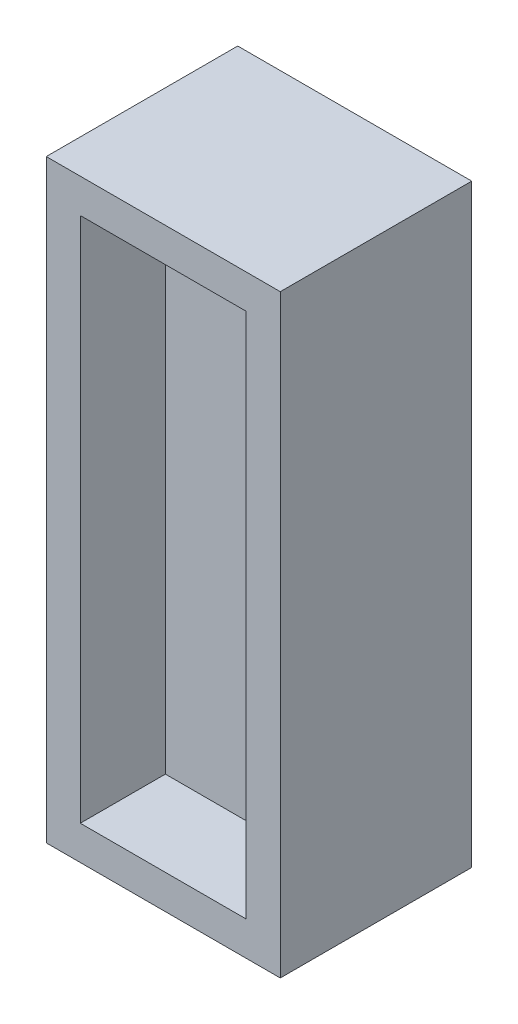
SolidWorks part; units mm, degrees
ref_plane "Front" through (0, 0, 0) normal (0, 0, 1) x (1, 0, 0)
ref_plane "Top" through (0, 0, 0) normal (0, 1, 0) x (1, 0, 0)
ref_plane "Right" through (0, 0, 0) normal (1, 0, 0) x (0, 0, -1)
sketch "Sketch1" plane through (0, 0, 0) normal (0, 0, 1) x (1, 0, 0)
  line L1 (27.5, -69.85) -> (-27.5, -69.85)
  line L2 (27.5, -69.85) -> (27.5, 69.85)
  line L3 (27.5, 69.85) -> (-27.5, 69.85)
  line L4 (-27.5, -69.85) -> (-27.5, 69.85)
  line L5 (27.5, -69.85) -> (-27.5, 69.85) construction
  line L6 (27.5, 69.85) -> (-27.5, -69.85) construction
  point P0 (0, 0)
  dimension "D1" = 55
  dimension "D2" = 139.7
extrude "Boss-Extrude1" add sketch "Sketch1" along normal blind 45
sketch "Sketch2" plane through (0, 0, 45) normal (0, 0, 1) x (1, 0, 0)
  line L0 (27.5, 69.85) -> (-27.5, 69.85) construction
  line L1 (-19.5, -61.85) -> (19.5, -61.85)
  line L2 (-19.5, -61.85) -> (-19.5, 61.85)
  line L3 (-19.5, 61.85) -> (19.5, 61.85)
  line L4 (19.5, -61.85) -> (19.5, 61.85)
  line L5 (-19.5, -61.85) -> (19.5, 61.85) construction
  line L6 (-19.5, 61.85) -> (19.5, -61.85) construction
  line L7 (27.5, -69.85) -> (27.5, 69.85) construction
  point P0 (0, 0)
  dimension "D1" = 8
  dimension "D2" = 8
extrude "Cut-Extrude1" cut sketch "Sketch2" against normal blind 20
